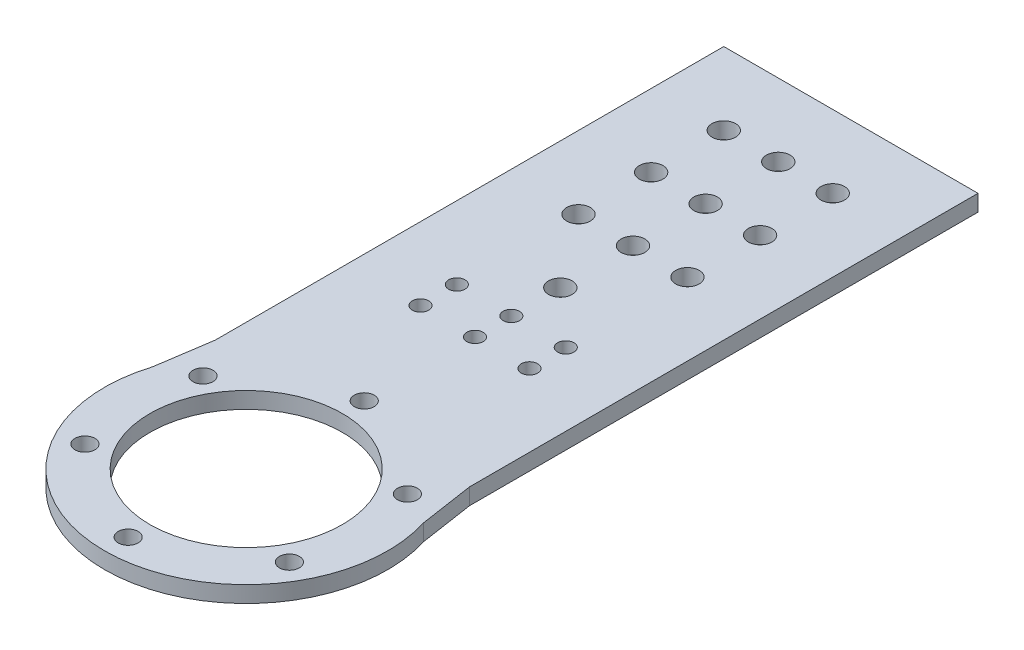
SolidWorks part; units mm, degrees
ref_plane "Front Plane" through (0, 0, 0) normal (0, 0, 1) x (1, 0, 0)
ref_plane "Top Plane" through (0, 0, 0) normal (0, 1, 0) x (1, 0, 0)
ref_plane "Right Plane" through (0, 0, 0) normal (1, 0, 0) x (0, 0, -1)
sketch "Sketch1" plane through (0, 0, 0) normal (0, 1, 0) x (1, 0, 0)
  circle A0 centre (0, 0) radius 45 construction
  circle A1 centre (0, 0) radius 39
  circle A2 centre (0, 0) radius 26.5
  circle A3 centre (0, 0) radius 32.5 construction
  dimension "D1" = 90
  dimension "D2" = 65
  dimension "D3" = 78
  dimension "D4" = 53
extrude "Boss-Extrude1" add sketch "Sketch1" along normal mid plane 4.5
sketch "Sketch3" plane through (0, 0, 0) normal (0, 1, 0) x (1, 0, 0)
  line L0 (0, 0) -> (0, 78) construction
  line L2 (-25, 78) -> (25, 78)
  line L3 (-25, 78) -> (-25, 26.5)
  line L4 (-25, 26.5) -> (25, 26.5)
  line L5 (25, 78) -> (25, 26.5)
  line L6 (0, 26.5) -> (0, 78) construction
  line L7 (-25, 52.25) -> (25, 52.25) construction
  circle A0 centre (0, 0) radius 26.5 construction
  point P3 (0, 52.25)
  dimension "D1" = 78
  dimension "D2" = 50
extrude "Boss-Extrude2" add sketch "Sketch3" along normal mid plane 4.5
sketch "Sketch4" plane through (0, 0, 0) normal (0, 1, 0) x (1, 0, 0)
  line L0 (-25, 53.9666) -> (-37.4668, 10.8276)
  line L1 (-25, 78) -> (-25, 29.9333) construction
  line L2 (-37.4668, 10.8276) -> (-25, 29.9333)
  line L3 (-25, 29.9333) -> (-25, 53.9666)
  line L4 (0, 0) -> (0, 78) construction
  line L5 (25, 78) -> (-25, 78) construction
  line L6 (37.4668, 10.8276) -> (25, 29.9333)
  line L7 (25, 53.9666) -> (37.4668, 10.8276)
  line L8 (25, 29.9333) -> (25, 53.9666)
  circle A0 centre (0, 0) radius 39 construction
extrude "Boss-Extrude3" [suppressed] add sketch "Sketch4" along normal mid plane 4.5
sketch "Sketch6" plane through (0, 0, 0) normal (0, 1, 0) x (1, 0, 0)
  line L0 (0, 0) -> (0, 96.5) construction
  line L1 (-35, 166.5) -> (-35, 26.5)
  line L2 (-35, 166.5) -> (35, 166.5)
  line L4 (35, 166.5) -> (35, 26.5)
  line L5 (0, 26.5) -> (0, 166.5) construction
  line L6 (-35, 96.5) -> (35, 96.5) construction
  line L7 (-35, 26.5) -> (-39, 0)
  line L8 (35, 26.5) -> (39, 0)
  line L9 (39, 0) -> (16.5208, 26.5)
  line L10 (16.5208, 26.5) -> (-14.9815, 26.5)
  line L11 (-14.9815, 26.5) -> (-39, 0)
  circle A0 centre (0, 0) radius 26.5 construction
  circle A1 centre (0, 0) radius 39 construction
  dimension "D1" = 70
  dimension "D2" = 140
extrude "Boss-Extrude4" add sketch "Sketch6" along normal mid plane 4.5
sketch "Sketch2" plane through (0, 0, 0) normal (0, 1, 0) x (1, 0, 0)
  circle A0 centre (0, 0) radius 32.5 construction
  circle A1 centre (0, 32.5) radius 2.75
  dimension "D1" = 65
  dimension "D2" = 5.5
extrude "Cut-Extrude1" cut sketch "Sketch2" against normal through all both and the other way through all contours A1
pattern_circular "CirPattern1" count 6 over 360 about axis through (0, 0, 0) along (0, 1, 0) of "Cut-Extrude1"
sketch "Sketch5" plane through (0, 2.25, 0) normal (0, 1, 0) x (1, 0, 0)
  line L0 (-25, 73) -> (25, 73) construction
  line L4 (35, 166.5) -> (-35, 166.5) construction
  circle A0 centre (0, 73) radius 2.25
  dimension "D1" = 4.5
  dimension "D3" = 93.5
extrude "Cut-Extrude2" cut sketch "Sketch5" against normal through all both and the other way through all
pattern_linear "LPattern1" count 2 spacing 15 along (1, 0, 0) count 2 spacing 10 along (0, 0, 1) of "Cut-Extrude2"
pattern_linear "LPattern2" count 2 spacing 15 along (-1, 0, 0) count 2 spacing 10 along (0, 0, 1) of "Cut-Extrude2"
sketch "Sketch7" plane through (0, 2.25, 0) normal (0, 1, 0) x (1, 0, 0)
  line L0 (0, 0) -> (0, 166.5) construction
  line L1 (35, 166.5) -> (-35, 166.5) construction
  line L2 (-15, 146.5) -> (15, 146.5) construction
  circle A0 centre (-15, 146.5) radius 3.25
  circle A1 centre (15, 146.5) radius 3.25
  point P8 (0, 146.5)
  dimension "D1" = 6.5
  dimension "D2" = 20
  dimension "D3" = 30
extrude "Cut-Extrude3" cut sketch "Sketch7" against normal through all both and the other way through all
pattern_linear "LPattern3" count 3 spacing 20 along (0, 0, 1) of "Cut-Extrude3"
sketch "Sketch8" plane through (0, 2.25, 0) normal (0, 1, 0) x (1, 0, 0)
  line L0 (0, 0) -> (0, 166.5) construction
  line L1 (35, 166.5) -> (-35, 166.5) construction
  circle A0 centre (0, 146.5) radius 3.25
  dimension "D1" = 6.5
  dimension "D2" = 20
extrude "Cut-Extrude4" cut sketch "Sketch8" against normal blind 10
pattern_linear "LPattern4" count 4 spacing 20 along (0, 0, 1) of "Cut-Extrude4"
